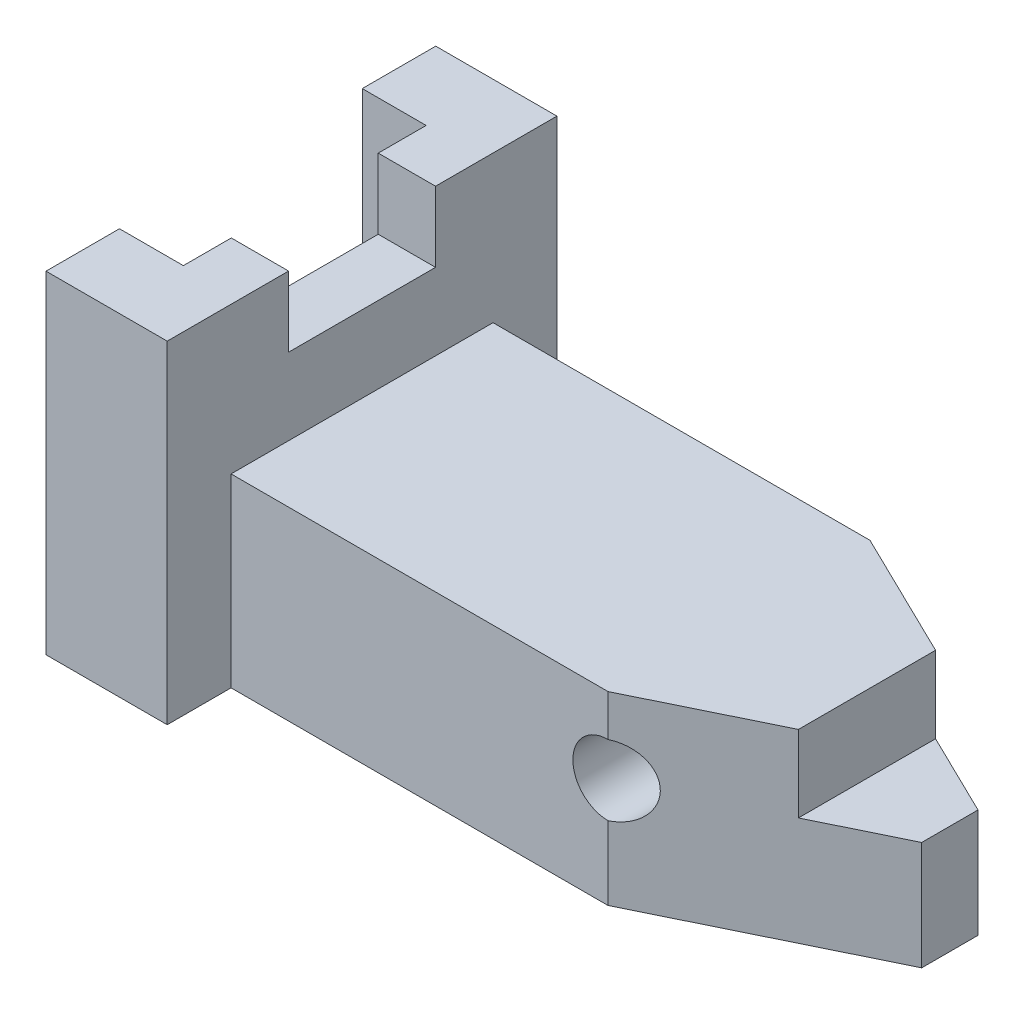
SolidWorks part; units mm, degrees
ref_plane "Front Plane" through (0, 0, 0) normal (0, 0, 1) x (1, 0, 0)
ref_plane "Top Plane" through (0, 0, 0) normal (0, 1, 0) x (1, 0, 0)
ref_plane "Right Plane" through (0, 0, 0) normal (1, 0, 0) x (0, 0, -1)
sketch "Sketch1" plane through (0, 0, 0) normal (0, 1, 0) x (1, 0, 0)
  line L0 (0, 30.5) -> (0, -30.5)
  line L1 (0, -30.5) -> (28, -30.5)
  line L2 (28, -30.5) -> (28, -20.5)
  line L3 (28, -20.5) -> (77.9688, -20.5)
  line L4 (77.9688, -20.5) -> (110.9688, -4.4048)
  line L5 (110.9688, 4.4048) -> (77.9688, 20.5)
  line L6 (77.9688, 20.5) -> (28, 20.5)
  line L7 (28, 20.5) -> (28, 30.5)
  line L8 (28, 30.5) -> (0, 30.5)
  line L9 (0, 0) -> (110.9688, 0) construction
  line L10 (110.9688, 4.4048) -> (110.9688, -4.4048)
  point P4 (0, 0)
  point P8 (120, 0)
  point P13 (0, 0)
  point P14 (74.2042, 22.3316)
  dimension "D1" = 33
  dimension "D2" = 26
  dimension "D3" = 26
  dimension "D4" = 28
  dimension "D5" = 61
  dimension "D6" = 120
  dimension "D7" = 10
extrude "Boss-Extrude1" add sketch "Sketch1" along normal blind 52
sketch "Sketch2" plane through (110.9688, 0, 0) normal (1, 0, 0) x (0, 0, -1)
  line L0 (-20.5, 29) -> (20.5, 29)
  line L1 (-20.5, 52) -> (-20.5, 0) construction
  line L2 (20.5, 52) -> (20.5, 0) construction
  line L3 (-20.5, 29) -> (-20.5, 52)
  line L4 (-20.5, 52) -> (20.5, 52)
  line L5 (20.5, 52) -> (20.5, 29)
  dimension "D1" = 23
extrude "Cut-Extrude1" cut sketch "Sketch2" against normal blind 92
sketch "Sketch3" plane through (28, 0, 0) normal (1, 0, 0) x (0, 0, -1)
  line L1 (-30.5, 0) -> (-20.5, 0)
  line L2 (-30.5, 0) -> (-30.5, 52)
  line L3 (-30.5, 52) -> (-20.5, 52)
  line L4 (-20.5, 0) -> (-20.5, 52)
  line L5 (20.5, 52) -> (30.5, 52)
  line L6 (20.5, 52) -> (20.5, 0)
  line L7 (20.5, 0) -> (30.5, 0)
  line L8 (30.5, 52) -> (30.5, 0)
extrude "Cut-Extrude2" cut sketch "Sketch3" against normal up to vertex
sketch "Sketch4" plane through (0, 52, 0) normal (0, 1, 0) x (1, 0, 0)
  line L0 (0, 30.5) -> (0, -30.5) construction
  line L1 (120, 0) -> (120, 12.4043)
  line L2 (120, 12.4043) -> (98, 12.4043)
  line L3 (98, 12.4043) -> (98, -13.2936)
  line L4 (98, -13.2936) -> (120, -13.2936)
  line L5 (120, -13.2936) -> (120, 0)
  point P0 (120, 0)
  dimension "D1" = 120
  dimension "D2" = 22
extrude "Cut-Extrude3" cut sketch "Sketch4" against normal blind 35
sketch "Sketch5" plane through (0, 52, 0) normal (0, 1, 0) x (1, 0, 0)
  line L1 (-10, -19) -> (10, -19)
  line L2 (-10, -19) -> (-10, 19)
  line L3 (-10, 19) -> (10, 19)
  line L4 (10, -19) -> (10, 19)
  line L5 (-10, -19) -> (10, 19) construction
  line L6 (-10, 19) -> (10, -19) construction
  point P0 (0, 0)
  dimension "D1" = 38
  dimension "D2" = 20
extrude "Cut-Extrude4" cut sketch "Sketch5" against normal blind 62
sketch "Sketch6" plane through (0, 52, 0) normal (0, 1, 0) x (1, 0, 0)
  line L0 (18.9688, -20.5) -> (18.9688, 20.5) construction
  line L1 (9.1524, -11.5) -> (18.9688, -11.5)
  line L2 (9.1524, -11.5) -> (9.1524, 11.5)
  line L3 (9.1524, 11.5) -> (18.9688, 11.5)
  line L4 (18.9688, -11.5) -> (18.9688, 11.5)
  line L5 (9.1524, -11.5) -> (18.9688, 11.5) construction
  line L6 (9.1524, 11.5) -> (18.9688, -11.5) construction
  point P0 (14.0606, 0)
  dimension "D1" = 23
extrude "Cut-Extrude5" cut sketch "Sketch6" against normal blind 11
sketch "Sketch8" plane through (0, 0, 20.5) normal (0, 0, 1) x (1, 0, 0)
  line L0 (77.9688, 29) -> (77.9688, 0) construction
  line L1 (18.9688, 0) -> (77.9688, 0) construction
  circle A0 centre (77.9688, 17) radius 5.5
  dimension "D2" = 11
  dimension "D1" = 17
extrude "Cut-Extrude6" cut sketch "Sketch8" against normal through all
sketch "Sketch9" plane through (10, 0, 0) normal (-1, 0, 0) x (0, 0, 1)
  line L0 (-20.5, 0) -> (20.5, 0)
  line L1 (-19, 0) -> (19, 0) construction
  line L2 (20.5, 0) -> (20.5, 29)
  line L3 (20.5, 29) -> (-20.5, 29)
  line L4 (-20.5, 29) -> (-20.5, 0)
  point P6 (0, 0)
  dimension "D1" = 41
  dimension "D2" = 29
